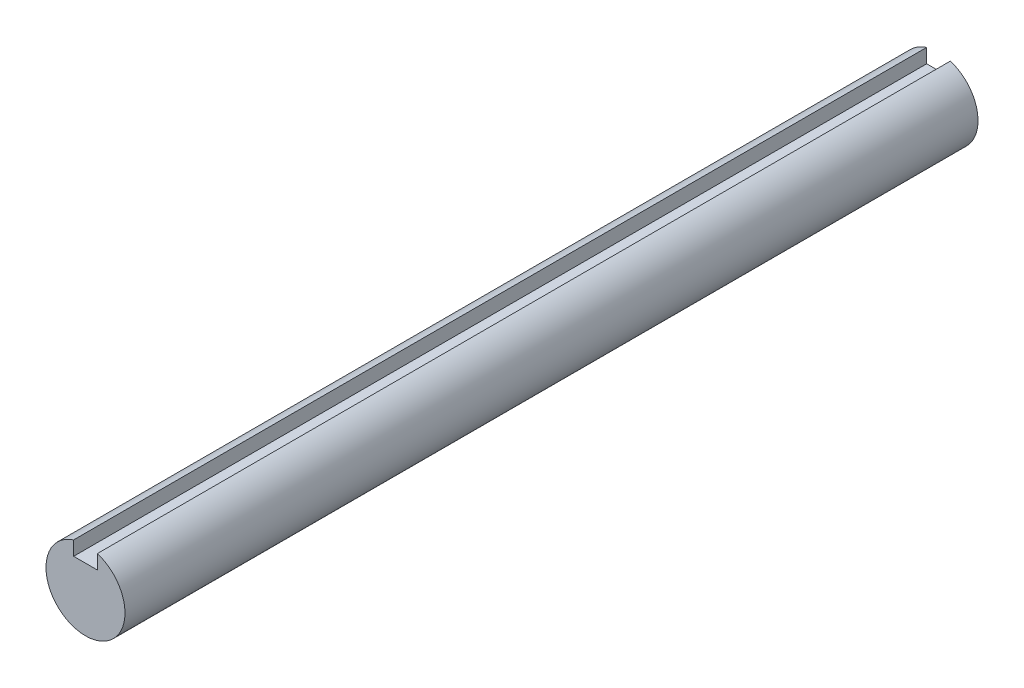
SolidWorks part; units mm, degrees
ref_plane "Front Plane" through (0, 0, 0) normal (0, 0, 1) x (1, 0, 0)
ref_plane "Top Plane" through (0, 0, 0) normal (0, 1, 0) x (1, 0, 0)
ref_plane "Right Plane" through (0, 0, 0) normal (1, 0, 0) x (0, 0, -1)
sketch "Sketch1" plane through (0, 0, 0) normal (1, 0, 0) x (0, 0, -1)
  line L0 (0, 0) -> (0, 5) construction
  line L1 (-53.975, 5) -> (53.975, 5)
  line L2 (-53.975, 5) -> (-53.975, -5)
  line L3 (-53.975, -5) -> (53.975, -5)
  line L4 (53.975, 5) -> (53.975, -5)
  line L5 (-53.975, 5) -> (53.975, -5) construction
  line L6 (-53.975, -5) -> (53.975, 5) construction
  line L7 (0, 0) -> (0, -5) construction
  point P0 (0, 0)
  point P8 (-42.475, 5)
  point P10 (42.475, 5)
  point P11 (-38.6417, -5)
  point P12 (40.696, -5)
  dimension "Diameter" = 10
  dimension "Length" = 107.95
  dimension "D1" = 11.5
  dimension "D2" = 11.5
  dimension "Keyway Length" = 107.95
  dimension "D3" = 13.279
  dimension "D5" = 15.3333
sketch "Sketch2" plane through (0, 0, 0) normal (0, 0, 1) x (1, 0, 0)
  line L0 (0, 0) -> (0, 5) construction
  line L2 (1.5, 2.9697) -> (-1.5, 2.9697)
  line L3 (1.5, 2.9697) -> (1.5, 4.7697)
  line L4 (1.5, 4.7697) -> (-1.5, 4.7697)
  line L5 (-1.5, 2.9697) -> (-1.5, 4.7697)
  line L6 (1.5, 2.9697) -> (-1.5, 4.7697) construction
  line L7 (1.5, 4.7697) -> (-1.5, 2.9697) construction
  circle A0 centre (0, 0) radius 5
  point P3 (0, 3.8697)
  dimension "Keyway Width" = 3
  dimension "Keyway Depth" = 1.8
sketch "Sketch3" plane through (0, 0, 0) normal (0, 0, 1) x (1, 0, 0)
  line L1 (-1.5, 2.9697) -> (-1.5, 4.7697) construction
  line L2 (1.5, 2.9697) -> (-1.5, 2.9697) construction
  line L3 (1.5, 2.9697) -> (1.5, 4.7697) construction
  line L5 (-1.5, 2.9697) -> (-1.5, 4.7697)
  line L6 (1.5, 2.9697) -> (-1.5, 2.9697)
  line L7 (1.5, 2.9697) -> (1.5, 4.7697)
  circle A0 centre (0, 0) radius 5 construction
  arc A1 (-1.5, 4.7697) -> (1.5, 4.7697) centre (0, 0) ccw
extrude "Boss-Extrude1" add sketch "Sketch3" along normal up to vertex (53.975 mm away) and the other way up to vertex (53.975 mm away) up to point (0, 5, 53.975) other way up to point (0, 5, -53.975)
chamfer "Chamfer1" [suppressed] distance 0.05 angle 45
hole_wizard "Tap Drill for #10-32 Tap1" [suppressed] positions "3DSketch1" profile "Sketch4" hole size "#10-32" standard "ANSI Inch"
sketch3d "3DSketch1" [suppressed]
  arc A0 (1.5, 4.7173, -39.6875) -> (-1.5, 4.7173, -39.6875) centre (0, 0, -39.6875) ccw construction
  arc A1 (-1.5, 4.7173, 39.6875) -> (1.5, 4.7173, 39.6875) centre (0, 0, 39.6875) ccw construction
  point P0 (0, 0, 39.6875)
  point P2 (0, 0, -39.6875)
  point P8 (0, 0, -44.6375)
  point P13 (0, 0, 44.6375)
sketch "Sketch4" plane through (0, 0, 39.6875) normal (1, 0, 0) x (0, -1, 0)
  line L0 (0, 0) -> (0, 12.3258)
  line L1 (0, 12.3258) -> (2.0193, 11.1125)
  line L2 (2.0193, 11.1125) -> (2.0193, 0)
  line L5 (2.0193, 0) -> (0, 0)
  line L10 (0, 12.3258) -> (-2.0193, 11.1125) construction
  line L11 (0, -6.35) -> (0, 107.95) construction
  dimension "Hole Dia." = 4.0386
  dimension "Hole Depth" = 11.1125
  dimension "Drill Angle" = 118
equation "\"D2@Sketch1\"=1.15*\"Diameter@Sketch1\""
equation "\"D1@Sketch1\"=\"D2@Sketch1\""
equation "\"D1@Chamfer1\"=\"Diameter@Sketch1\"*.005"
equation "\"D3@Sketch1\"=\"D2@Sketch1\"/(2*tan(.5236*180/pi))*4/3"
equation "\"D5@Sketch1\" = 4 / 3 * \"D2@Sketch1\""
